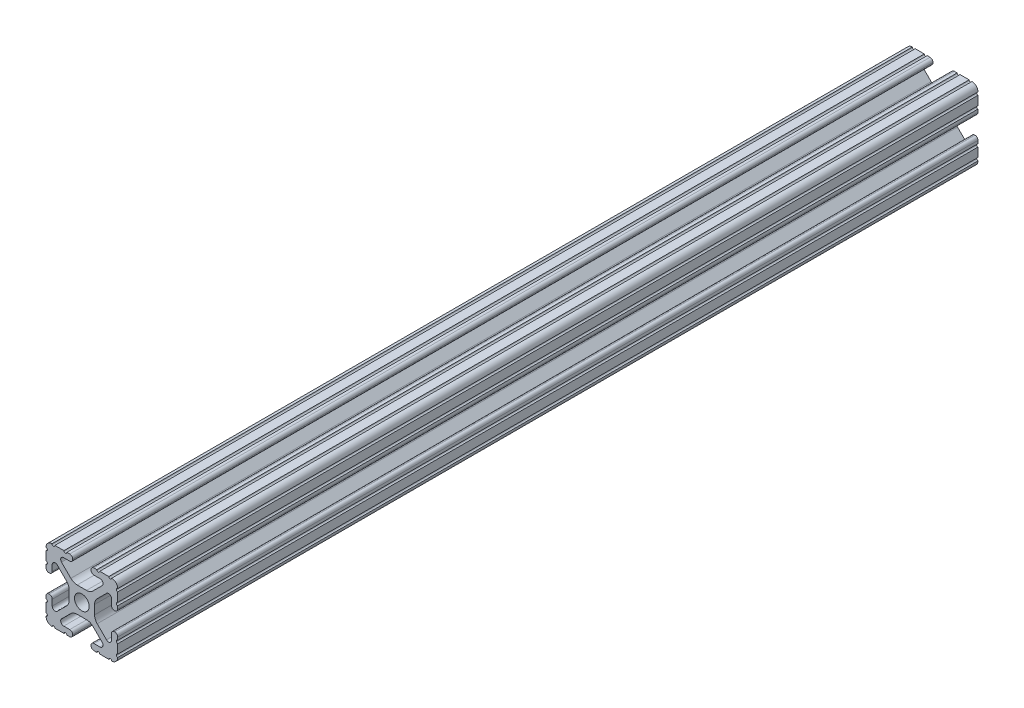
SolidWorks part; units mm, degrees
ref_plane "Front Plane" through (0, 0, 0) normal (0, 0, 1) x (1, 0, 0)
ref_plane "Top Plane" through (0, 0, 0) normal (0, 1, 0) x (1, 0, 0)
ref_plane "Right Plane" through (0, 0, 0) normal (1, 0, 0) x (0, 0, -1)
sketch "Sketch1" plane through (0, 0, 0) normal (0, 0, 1) x (1, 0, 0)
  line L88 (-7.1797, -8.6452) -> (-3.9523, -5.4237)
  line L89 (-1.7093, -4.4958) -> (1.7093, -4.4958)
  line L90 (3.9523, -5.4237) -> (7.1797, -8.6452)
  line L91 (6.4164, -10.4902) -> (4.2875, -10.4902)
  line L92 (3.2385, -11.5392) -> (3.2385, -11.651)
  line L93 (4.2875, -12.7) -> (5.3171, -12.7)
  line L94 (6.3331, -12.7) -> (9.5504, -12.7)
  line L95 (12.7, -9.5504) -> (12.7, -6.3331)
  line L96 (12.7, -5.3171) -> (12.7, -4.2875)
  line L97 (11.651, -3.2385) -> (11.5392, -3.2385)
  line L98 (10.4902, -4.2875) -> (10.4902, -6.4021)
  line L99 (8.7371, -7.1294) -> (5.441, -3.8408)
  line L100 (4.5085, -1.5932) -> (4.5085, 1.5932)
  line L101 (5.441, 3.8408) -> (8.7371, 7.1294)
  line L102 (10.4902, 6.4021) -> (10.4902, 4.2875)
  line L103 (11.5392, 3.2385) -> (11.651, 3.2385)
  line L104 (12.7, 4.2875) -> (12.7, 5.3171)
  line L105 (12.7, 6.3331) -> (12.7, 9.5504)
  line L106 (9.5504, 12.7) -> (6.3331, 12.7)
  line L107 (5.3171, 12.7) -> (4.2875, 12.7)
  line L108 (3.2385, 11.651) -> (3.2385, 11.5392)
  line L109 (4.2875, 10.4902) -> (6.4768, 10.4902)
  line L110 (7.207, 8.7244) -> (3.8983, 5.4232)
  line L111 (1.6558, 4.4958) -> (-1.6558, 4.4958)
  line L112 (-3.8983, 5.4232) -> (-7.207, 8.7244)
  line L113 (-6.4768, 10.4902) -> (-4.2875, 10.4902)
  line L114 (-3.2385, 11.5392) -> (-3.2385, 11.651)
  line L115 (-4.2875, 12.7) -> (-5.3171, 12.7)
  line L116 (-6.3331, 12.7) -> (-9.5504, 12.7)
  line L117 (-12.7, 9.5504) -> (-12.7, 6.3331)
  line L118 (-12.7, 5.3171) -> (-12.7, 4.2875)
  line L119 (-11.651, 3.2385) -> (-11.5392, 3.2385)
  line L120 (-10.4902, 4.2875) -> (-10.4902, 6.4021)
  line L121 (-8.7371, 7.1294) -> (-5.441, 3.8408)
  line L122 (-4.5085, 1.5932) -> (-4.5085, -1.5932)
  line L123 (-5.441, -3.8408) -> (-8.7371, -7.1294)
  line L124 (-10.4902, -6.4021) -> (-10.4902, -4.2875)
  line L125 (-11.5392, -3.2385) -> (-11.651, -3.2385)
  line L126 (-12.7, -4.2875) -> (-12.7, -5.3171)
  line L127 (-12.7, -6.3331) -> (-12.7, -9.5504)
  line L128 (-9.5504, -12.7) -> (-6.3331, -12.7)
  line L129 (-5.3171, -12.7) -> (-4.2875, -12.7)
  line L130 (-3.2385, -11.651) -> (-3.2385, -11.5392)
  line L131 (-4.2875, -10.4902) -> (-6.4164, -10.4902)
  circle A1 centre (0, 0) radius 2.6035
  arc A104 (-7.1797, -8.6452) -> (-6.4164, -10.4902) centre (-6.4164, -9.4098) ccw
  arc A105 (-1.7093, -4.4958) -> (-3.9523, -5.4237) centre (-1.7093, -7.6708) ccw
  arc A106 (3.9523, -5.4237) -> (1.7093, -4.4958) centre (1.7093, -7.6708) ccw
  arc A107 (6.4164, -10.4902) -> (7.1797, -8.6452) centre (6.4164, -9.4098) ccw
  arc A108 (4.2875, -10.4902) -> (3.2385, -11.5392) centre (4.2875, -11.5392) ccw
  arc A109 (3.2385, -11.651) -> (4.2875, -12.7) centre (4.2875, -11.651) ccw
  arc A110 (6.3331, -12.7) -> (5.3171, -12.7) centre (5.8251, -12.7) ccw
  arc A111 (10.5664, -12.6998) -> (9.5504, -12.7) centre (10.0584, -12.7) ccw
  arc A112 (10.5664, -12.6998) -> (12.6998, -10.5664) centre (10.5918, -10.5918) ccw
  arc A113 (12.7, -9.5504) -> (12.6998, -10.5664) centre (12.7, -10.0584) ccw
  arc A114 (12.7, -5.3171) -> (12.7, -6.3331) centre (12.7, -5.8251) ccw
  arc A115 (12.7, -4.2875) -> (11.651, -3.2385) centre (11.651, -4.2875) ccw
  arc A116 (11.5392, -3.2385) -> (10.4902, -4.2875) centre (11.5392, -4.2875) ccw
  arc A117 (8.7371, -7.1294) -> (10.4902, -6.4021) centre (9.4628, -6.4021) ccw
  arc A118 (4.5085, -1.5932) -> (5.441, -3.8408) centre (7.6835, -1.5932) ccw
  arc A119 (5.441, 3.8408) -> (4.5085, 1.5932) centre (7.6835, 1.5932) ccw
  arc A120 (10.4902, 6.4021) -> (8.7371, 7.1294) centre (9.4628, 6.4021) ccw
  arc A121 (10.4902, 4.2875) -> (11.5392, 3.2385) centre (11.5392, 4.2875) ccw
  arc A122 (11.651, 3.2385) -> (12.7, 4.2875) centre (11.651, 4.2875) ccw
  arc A123 (12.7, 6.3331) -> (12.7, 5.3171) centre (12.7, 5.8251) ccw
  arc A124 (12.6998, 10.5664) -> (12.7, 9.5504) centre (12.7, 10.0584) ccw
  arc A125 (12.6998, 10.5664) -> (10.5664, 12.6998) centre (10.5918, 10.5918) ccw
  arc A126 (9.5504, 12.7) -> (10.5664, 12.6998) centre (10.0584, 12.7) ccw
  arc A127 (5.3171, 12.7) -> (6.3331, 12.7) centre (5.8251, 12.7) ccw
  arc A128 (4.2875, 12.7) -> (3.2385, 11.651) centre (4.2875, 11.651) ccw
  arc A129 (3.2385, 11.5392) -> (4.2875, 10.4902) centre (4.2875, 11.5392) ccw
  arc A130 (7.207, 8.7244) -> (6.4768, 10.4902) centre (6.4768, 9.4563) ccw
  arc A131 (1.6558, 4.4958) -> (3.8983, 5.4232) centre (1.6558, 7.6708) ccw
  arc A132 (-3.8983, 5.4232) -> (-1.6558, 4.4958) centre (-1.6558, 7.6708) ccw
  arc A133 (-6.4768, 10.4902) -> (-7.207, 8.7244) centre (-6.4768, 9.4563) ccw
  arc A134 (-4.2875, 10.4902) -> (-3.2385, 11.5392) centre (-4.2875, 11.5392) ccw
  arc A135 (-3.2385, 11.651) -> (-4.2875, 12.7) centre (-4.2875, 11.651) ccw
  arc A136 (-6.3331, 12.7) -> (-5.3171, 12.7) centre (-5.8251, 12.7) ccw
  arc A137 (-10.5664, 12.6998) -> (-9.5504, 12.7) centre (-10.0584, 12.7) ccw
  arc A138 (-10.5664, 12.6998) -> (-12.6998, 10.5664) centre (-10.5918, 10.5918) ccw
  arc A139 (-12.7, 9.5504) -> (-12.6998, 10.5664) centre (-12.7, 10.0584) ccw
  arc A140 (-12.7, 5.3171) -> (-12.7, 6.3331) centre (-12.7, 5.8251) ccw
  arc A141 (-12.7, 4.2875) -> (-11.651, 3.2385) centre (-11.651, 4.2875) ccw
  arc A142 (-11.5392, 3.2385) -> (-10.4902, 4.2875) centre (-11.5392, 4.2875) ccw
  arc A143 (-8.7371, 7.1294) -> (-10.4902, 6.4021) centre (-9.4628, 6.4021) ccw
  arc A144 (-4.5085, 1.5932) -> (-5.441, 3.8408) centre (-7.6835, 1.5932) ccw
  arc A145 (-5.441, -3.8408) -> (-4.5085, -1.5932) centre (-7.6835, -1.5932) ccw
  arc A146 (-10.4902, -6.4021) -> (-8.7371, -7.1294) centre (-9.4628, -6.4021) ccw
  arc A147 (-10.4902, -4.2875) -> (-11.5392, -3.2385) centre (-11.5392, -4.2875) ccw
  arc A148 (-11.651, -3.2385) -> (-12.7, -4.2875) centre (-11.651, -4.2875) ccw
  arc A149 (-12.7, -6.3331) -> (-12.7, -5.3171) centre (-12.7, -5.8251) ccw
  arc A150 (-12.6998, -10.5664) -> (-12.7, -9.5504) centre (-12.7, -10.0584) ccw
  arc A151 (-12.6998, -10.5664) -> (-10.5664, -12.6998) centre (-10.5918, -10.5918) ccw
  arc A152 (-9.5504, -12.7) -> (-10.5664, -12.6998) centre (-10.0584, -12.7) ccw
  arc A153 (-5.3171, -12.7) -> (-6.3331, -12.7) centre (-5.8251, -12.7) ccw
  arc A154 (-4.2875, -12.7) -> (-3.2385, -11.651) centre (-4.2875, -11.651) ccw
  arc A155 (-3.2385, -11.5392) -> (-4.2875, -10.4902) centre (-4.2875, -11.5392) ccw
extrude "Boss-Extrude1" add sketch "Sketch1" along normal mid plane 304.8
